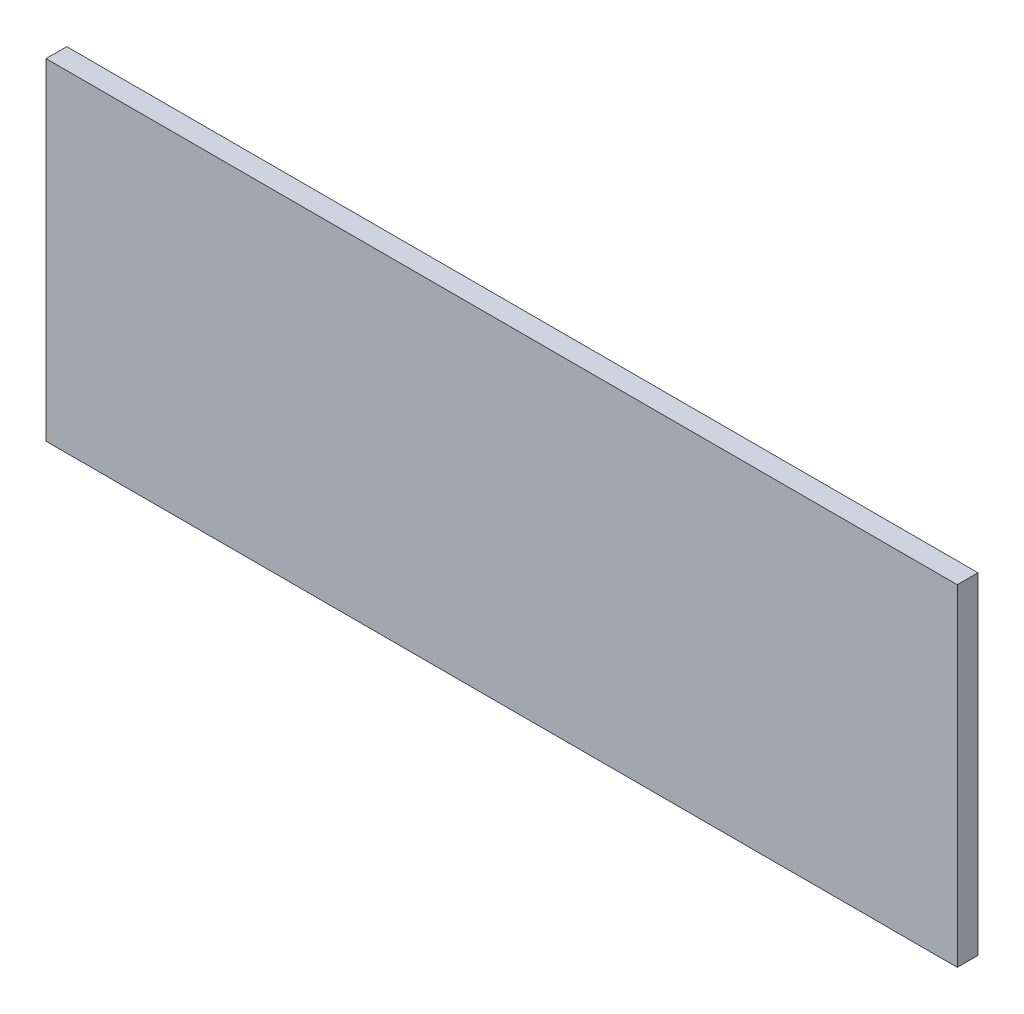
SolidWorks part; units mm, degrees
ref_plane "Front Plane" through (0, 0, 0) normal (0, 0, 1) x (1, 0, 0)
ref_plane "Top Plane" through (0, 0, 0) normal (0, 1, 0) x (1, 0, 0)
ref_plane "Right Plane" through (0, 0, 0) normal (1, 0, 0) x (0, 0, -1)
sketch "Sketch1" plane through (0, 0, 0) normal (0, 0, 1) x (1, 0, 0)
  line L1 (-69.85, -25.4) -> (69.85, -25.4)
  line L2 (-69.85, -25.4) -> (-69.85, 25.4)
  line L3 (-69.85, 25.4) -> (69.85, 25.4)
  line L4 (69.85, -25.4) -> (69.85, 25.4)
  line L5 (-69.85, -25.4) -> (69.85, 25.4) construction
  line L6 (-69.85, 25.4) -> (69.85, -25.4) construction
  point P0 (0, 0)
  dimension "D1" = 50.8
  dimension "D2" = 139.7
extrude "Boss-Extrude1" add sketch "Sketch1" along normal mid plane 3.175
